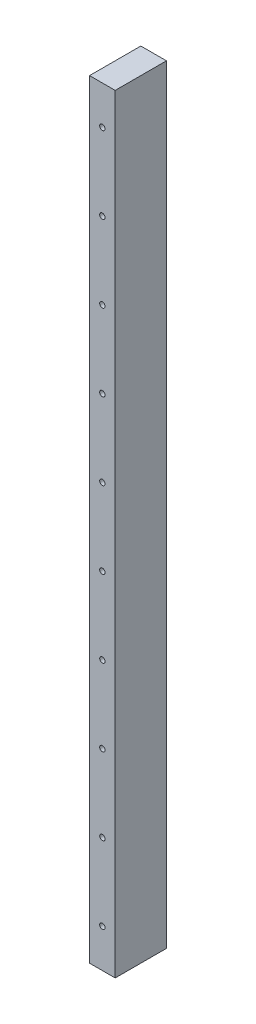
SolidWorks part; units mm, degrees
ref_plane "前视基准面" through (0, 0, 0) normal (0, 0, 1) x (1, 0, 0)
ref_plane "上视基准面" through (0, 0, 0) normal (0, 1, 0) x (1, 0, 0)
ref_plane "右视基准面" through (0, 0, 0) normal (1, 0, 0) x (0, 0, -1)
ref_plane "基准面1" through (-230, 0, 0) normal (1, 0, 0) x (0, 0, -1)
sketch "草图1" plane through (-230, 0, 0) normal (1, 0, 0) x (0, 0, -1)
  line L0 (175, 1220) -> (175, 1820)
  line L1 (175, 1820) -> (135, 1820)
  line L2 (135, 1820) -> (135, 1220)
  line L3 (135, 1220) -> (175, 1220)
extrude "凸台-拉伸1" add sketch "草图1" against normal blind 20
hole_wizard "Ø9.0 (9) 直径孔1" positions "草图3" profile "草图2" hole size "Ø9.0" standard "ANSI Metric"
sketch "草图3" plane through (0, 0, -175) normal (0, 0, -1) x (-1, 0, 0)
  point P0 (240, 1250)
  point P1 (240, 1430)
  point P2 (240, 1610)
  point P3 (240, 1790)
sketch "草图2" plane through (-240, 1250, -175) normal (1, 0, 0) x (0, 1, 0)
  line L0 (0, 0) -> (0, 17.7039)
  line L1 (0, 17.7039) -> (4.5, 15)
  line L2 (4.5, 15) -> (4.5, 0)
  line L5 (4.5, 0) -> (0, 0)
  line L10 (0, 17.7039) -> (-4.5, 15) construction
  line L11 (0, -6.35) -> (0, 107.95) construction
  dimension "孔直径" = 9
  dimension "孔深度" = 15
  dimension "导头角度" = 118
hole_wizard "Ø4.2 (4.2) 直径孔1" positions "草图5" profile "草图4" hole size "Ø4.2" standard "ANSI Metric"
sketch "草图5" plane through (0, 0, -135) normal (0, 0, 1) x (1, 0, 0)
  point P0 (-240, 1610)
  point P1 (-240, 1250)
  point P2 (-240, 1310)
  point P3 (-240, 1370)
  point P4 (-240, 1430)
  point P5 (-240, 1490)
  point P6 (-240, 1550)
  point P7 (-240, 1670)
  point P8 (-240, 1730)
  point P9 (-240, 1790)
sketch "草图4" plane through (-240, 1610, -135) normal (1, 0, 0) x (0, -1, 0)
  line L0 (0, 0) -> (0, 13.6618)
  line L1 (0, 13.6618) -> (2.1, 12.4)
  line L2 (2.1, 12.4) -> (2.1, 0)
  line L5 (2.1, 0) -> (0, 0)
  line L10 (0, 13.6618) -> (-2.1, 12.4) construction
  line L11 (0, -6.35) -> (0, 107.95) construction
  dimension "孔直径" = 4.2
  dimension "孔深度" = 12.4
  dimension "导头角度" = 118
